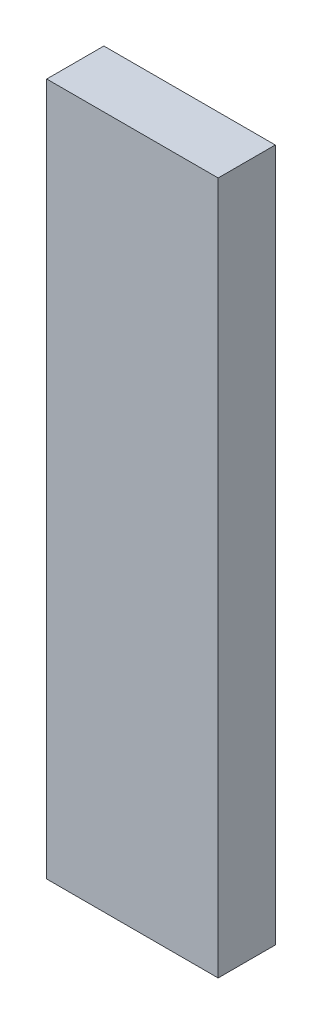
SolidWorks part; units mm, degrees
ref_plane "Front Plane" through (0, 0, 0) normal (0, 0, 1) x (1, 0, 0)
ref_plane "Top Plane" through (0, 0, 0) normal (0, 1, 0) x (1, 0, 0)
ref_plane "Right Plane" through (0, 0, 0) normal (1, 0, 0) x (0, 0, -1)
sketch "Sketch1" plane through (0, 0, 0) normal (0, 1, 0) x (1, 0, 0)
  line L1 (0, 0) -> (38.1, 0)
  line L2 (0, 0) -> (0, 12.7)
  line L3 (0, 12.7) -> (38.1, 12.7)
  line L4 (38.1, 0) -> (38.1, 12.7)
  dimension "D1" = 38.1
  dimension "D2" = 12.7
extrude "Boss-Extrude1" add sketch "Sketch1" along normal blind 154
